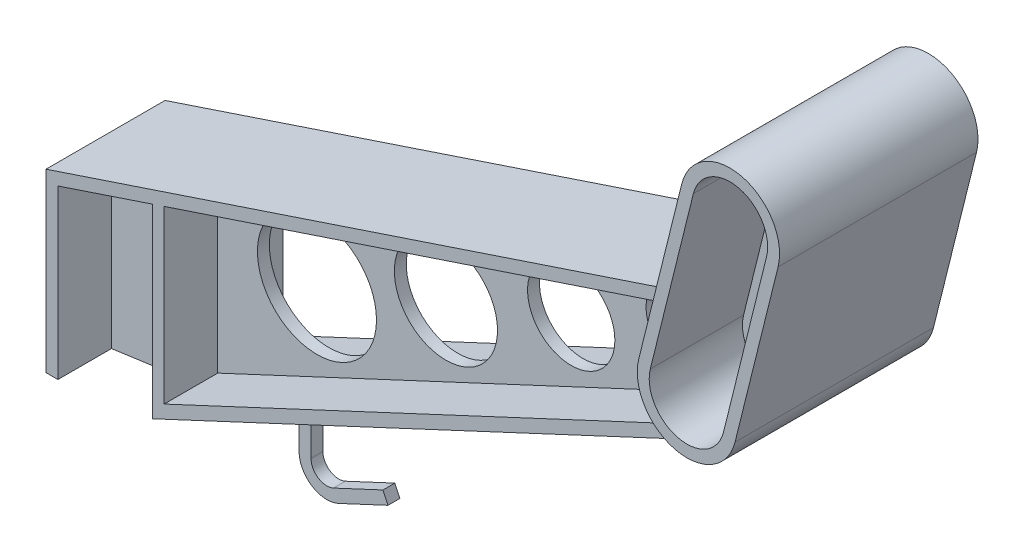
SolidWorks part; units mm, degrees
ref_plane "Piano frontale" through (0, 0, 0) normal (0, 0, 1) x (1, 0, 0)
ref_plane "Piano superiore" through (0, 0, 0) normal (0, 1, 0) x (1, 0, 0)
ref_plane "Piano destro" through (0, 0, 0) normal (1, 0, 0) x (0, 0, -1)
sketch "Schizzo1" plane through (0, 0, 0) normal (0, 0, 1) x (1, 0, 0)
  line L0 (-61.9531, -55.1429) -> (-61.9531, -5.1429)
  line L1 (-61.9531, -5.1429) -> (88.0469, 44.8571)
  line L2 (88.0469, 44.8571) -> (88.0469, 14.8571)
  line L3 (88.0469, 14.8571) -> (-61.9531, -55.1429)
  point P3 (0, 0)
  dimension "D1" = 50
  dimension "D2" = 30
  dimension "D3" = 150
  dimension "D4" = 70
extrude "Estrusione-Estrusione1" add sketch "Schizzo1" along normal mid plane 30 contours L3 L0 L1 L2
sketch "Schizzo2" plane through (0, 0, 15) normal (0, 0, 1) x (1, 0, 0)
  line L8 (85.0469, 16.7677) -> (85.0469, 40.6948)
  line L9 (85.0469, 40.6948) -> (-58.9531, -7.3052)
  line L10 (-58.9531, -7.3052) -> (-58.9531, -50.4323)
  line L11 (-58.9531, -50.4323) -> (85.0469, 16.7677)
  line L12 (85.0469, 16.7677) -> (85.0469, 40.6948)
  line L13 (85.0469, 40.6948) -> (-58.9531, -7.3052)
  line L14 (-58.9531, -7.3052) -> (-58.9531, -50.4323)
  line L15 (-58.9531, -50.4323) -> (85.0469, 16.7677)
  dimension "D1" = 3
extrude "Taglio-Estrusione1" cut sketch "Schizzo2" against normal offset from surface (13.5 mm away) 1.5 contours L12 L13 L14 L15 up to plane "Piano frontale"
mirror "Specchia1" about plane through (0, 0, 0) normal (0, 0, 1) of "Taglio-Estrusione1"
sketch "Schizzo3" plane through (0, 0, 1.5) normal (0, 0, 1) x (1, 0, 0)
  line L0 (-58.9531, -28.8688) -> (85.0469, 28.7312) construction
  line L1 (-58.9531, -7.3052) -> (-58.9531, -50.4323) construction
  line L2 (85.0469, 40.6948) -> (85.0469, 16.7677) construction
  circle A0 centre (-33.9531, -18.8688) radius 15
  circle A1 centre (-1.4564, -5.8701) radius 13
  circle A2 centre (30.1118, 6.7572) radius 11
  circle A3 centre (57.9661, 17.8989) radius 9
  point P14 (0, 0)
  point P15 (0, 0)
  point P16 (-3.9057, 28.4595)
  point P17 (0, 0)
  point P19 (-27.9218, 32.6976)
  dimension "D1" = 30
  dimension "D2" = 26
  dimension "D3" = 22
  dimension "D4" = 18
  dimension "D5" = 35
  dimension "D6" = 34
  dimension "D7" = 30
  dimension "D8" = 25
extrude "Taglio-Estrusione2" cut sketch "Schizzo3" against normal through all contours A0 | A1 | A2 | A3
sketch "Schizzo4" plane through (0, 0, 0) normal (0, 0, 1) x (1, 0, 0)
  line L0 (82.7608, 26.1844) -> (93.6095, 69.8571) construction
  line L1 (70.6295, 29.1979) -> (81.4782, 72.8706)
  line L2 (94.8921, 23.1708) -> (105.7408, 66.8436)
  line L5 (88.0469, 14.8571) -> (-61.9531, -55.1429) construction
  arc A0 (70.6295, 29.1979) -> (94.8921, 23.1708) centre (82.7608, 26.1844) ccw
  arc A1 (105.7408, 66.8436) -> (81.4782, 72.8706) centre (93.6095, 69.8571) ccw
  point P2 (88.1852, 48.0207)
  point P14 (75.8897, 70.6567)
  point P15 (93.6564, 69.8454)
  point P16 (84.1124, 71.1641)
  point P17 (91.6205, 70.3036)
  point P18 (0, 0)
  dimension "D1" = 25
  dimension "D2" = 45
  dimension "D3" = 55
extrude "Estrusione-Estrusione3" add sketch "Schizzo4" along normal mid plane 50
sketch "Schizzo5" plane through (0, 0, 25) normal (0, 0, 1) x (1, 0, 0)
  line L4 (91.9806, 23.8941) -> (102.8293, 67.5668)
  line L5 (84.3897, 72.1474) -> (73.541, 28.4747)
  line L6 (91.9806, 23.8941) -> (102.8293, 67.5668)
  line L7 (84.3897, 72.1474) -> (73.541, 28.4747)
  arc A4 (73.541, 28.4747) -> (91.9806, 23.8941) centre (82.7608, 26.1844) ccw
  arc A5 (102.8293, 67.5668) -> (84.3897, 72.1474) centre (93.6095, 69.8571) ccw
  arc A6 (73.541, 28.4747) -> (91.9806, 23.8941) centre (82.7608, 26.1844) ccw
  arc A7 (102.8293, 67.5668) -> (84.3897, 72.1474) centre (93.6095, 69.8571) ccw
  dimension "D1" = 3
extrude "Taglio-Estrusione4" cut sketch "Schizzo5" against normal up to surface (23.5 mm away) contours A6 L6 A7 L7 up to face at (11.5436, -5.8701, 1.5)
sketch "Schizzo6" plane through (0, 0, -25) normal (0, 0, -1) x (-1, 0, 0)
  line L4 (-73.541, 28.4747) -> (-84.3897, 72.1474)
  line L5 (-102.8293, 67.5668) -> (-91.9806, 23.8941)
  line L6 (-73.541, 28.4747) -> (-84.3897, 72.1474)
  line L7 (-102.8293, 67.5668) -> (-91.9806, 23.8941)
  arc A4 (-91.9806, 23.8941) -> (-73.541, 28.4747) centre (-82.7608, 26.1844) ccw
  arc A5 (-84.3897, 72.1474) -> (-102.8293, 67.5668) centre (-93.6095, 69.8571) ccw
  arc A6 (-91.9806, 23.8941) -> (-73.541, 28.4747) centre (-82.7608, 26.1844) ccw
  arc A7 (-84.3897, 72.1474) -> (-102.8293, 67.5668) centre (-93.6095, 69.8571) ccw
  dimension "D1" = 3
extrude "Taglio-Estrusione5" cut sketch "Schizzo6" against normal up to surface (23.5 mm away) contours A6 L6 A7 L7 up to face at (66.9661, 17.8989, -1.5)
sketch "Schizzo7" plane through (0, 0, 1.5) normal (0, 0, 1) x (1, 0, 0)
  line L0 (82.7608, 26.1844) -> (93.6095, 69.8571) construction
  line L1 (76.9378, 27.6309) -> (87.7865, 71.3036)
  line L2 (88.5839, 24.7379) -> (99.4326, 68.4106)
  line L5 (82.7608, 26.1844) -> (93.6095, 69.8571) construction
  arc A0 (76.9378, 27.6309) -> (88.5839, 24.7379) centre (82.7608, 26.1844) ccw
  arc A1 (99.4326, 68.4106) -> (87.7865, 71.3036) centre (93.6095, 69.8571) ccw
  point P2 (88.1852, 48.0207)
  point P7 (93.8456, 65.1702)
  point P8 (89.7251, 49.1336)
  point P9 (0, 0)
  point P10 (88.1852, 48.0207)
  point P11 (0, 0)
  point P12 (88.1852, 48.0207)
  point P16 (82.7608, 26.1844)
  point P18 (0, 0)
  dimension "D1" = 12
  dimension "D2" = 45
extrude "Taglio-Estrusione6" cut sketch "Schizzo7" against normal through all
sketch "Schizzo8" plane through (0, 0, 0) normal (0, 0, 1) x (1, 0, 0)
  line L0 (-61.9531, -5.1429) -> (-88.7275, -14.0677)
  line L1 (-88.7275, -14.0677) -> (-88.7275, -58.4706)
  line L2 (-61.9531, -5.1429) -> (73.2982, 39.9408) construction
  point P6 (-88.7275, -58.4706)
extrude "Estrusione-Sottile2" add sketch "Schizzo8" along normal up to surface and the other way up to surface thin
sketch "Schizzo9" plane through (0, 0, 0) normal (0, 0, 1) x (1, 0, 0)
  line L0 (-85.7275, -58.4706) -> (-61.9531, -55.1429)
  line L1 (-61.9531, -55.1429) -> (-61.9531, -8.3052)
  line L2 (-61.9531, -8.3052) -> (-85.7275, -16.23)
  line L3 (-85.7275, -16.23) -> (-85.7275, -58.4706)
extrude "Estrusione-Estrusione4" add sketch "Schizzo9" along normal mid plane 3
sketch "Schizzo10" plane through (-4.6524, 13.9573, 0) normal (-0.3162, 0.9487, 0) x (0.9487, 0.3162, 0)
  line L0 (-88.6229, -15) -> (-88.6229, -5)
  line L1 (-88.6229, -15) -> (-88.6229, 15) construction
  line L2 (-88.6229, -5) -> (-65.0838, -15)
  line L3 (-88.6229, -15) -> (82.1671, -15) construction
  line L4 (-65.0838, -15) -> (-88.6229, -15)
  dimension "D1" = 10
sketch "Schizzo11" plane through (0, 0, 0) normal (0, 0, 1) x (1, 0, 0)
  line L0 (-33.9531, -42.0763) -> (-33.9531, -55.7955)
  line L1 (88.0469, 14.8571) -> (-61.9531, -55.1429) construction
  line L2 (-28.2616, -59.4202) -> (-15.8294, -53.6185)
  line L3 (-33.9531, -18.9912) -> (-33.9531, -76.6248) construction
  arc A0 (-28.2616, -59.4202) -> (-33.9531, -55.7955) centre (-29.9531, -55.7955) cw
  point P8 (-33.9531, -62.0763)
  point P11 (-33.9531, -42.0763)
  dimension "D3" = 4
  dimension "D1" = 20
  dimension "D2" = 20
extrude "Estrusione-Sottile3" add sketch "Schizzo11" along normal blind 3 thin
